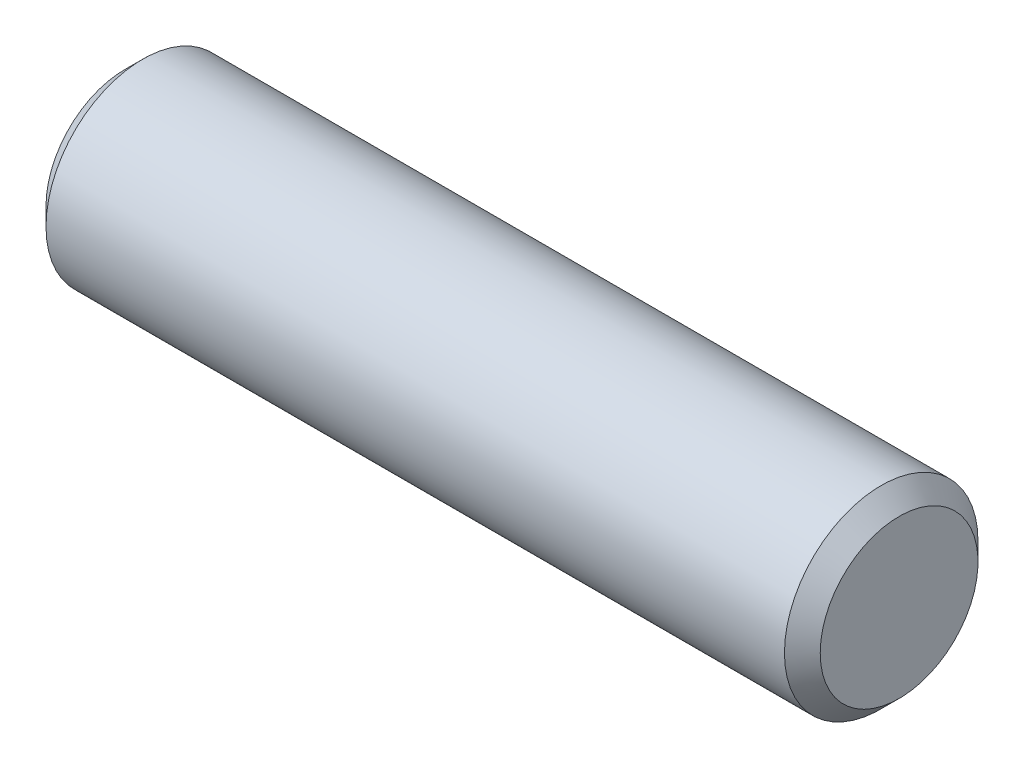
SolidWorks part; units mm, degrees
ref_plane "Plane1" through (0, 0, 0) normal (0, 0, 1) x (1, 0, 0)
ref_plane "Plane2" through (0, 0, 0) normal (0, 1, 0) x (1, 0, 0)
ref_plane "Plane3" through (0, 0, 0) normal (1, 0, 0) x (0, 0, -1)
sketch "BodySke" plane through (0, 0, 0) normal (0, 0, 1) x (1, 0, 0)
  line L1 (-12, 2.4455) -> (-12, 0)
  line L2 (-12, 2.4455) -> (-11.4455, 3)
  line L3 (-11.4455, 3) -> (11.4455, 3)
  line L4 (12, 2.4455) -> (12, 0)
  line L5 (12, 0) -> (-12, 0)
  line L6 (0, 0) -> (127, 0) construction
  line L8 (12, 2.4455) -> (11.4455, 3)
  line L10 (12, -2.4455) -> (11.4455, -3) construction
  line L13 (0, 3) -> (0, -3.175) construction
  dimension "D1" = 24
  dimension "Diameter" = 6
  dimension "Body_ch_ang" = 45
  dimension "Minor_dia" = 4.891
revolve "BaseBody" add sketch "BodySke" angle 360 about L6
